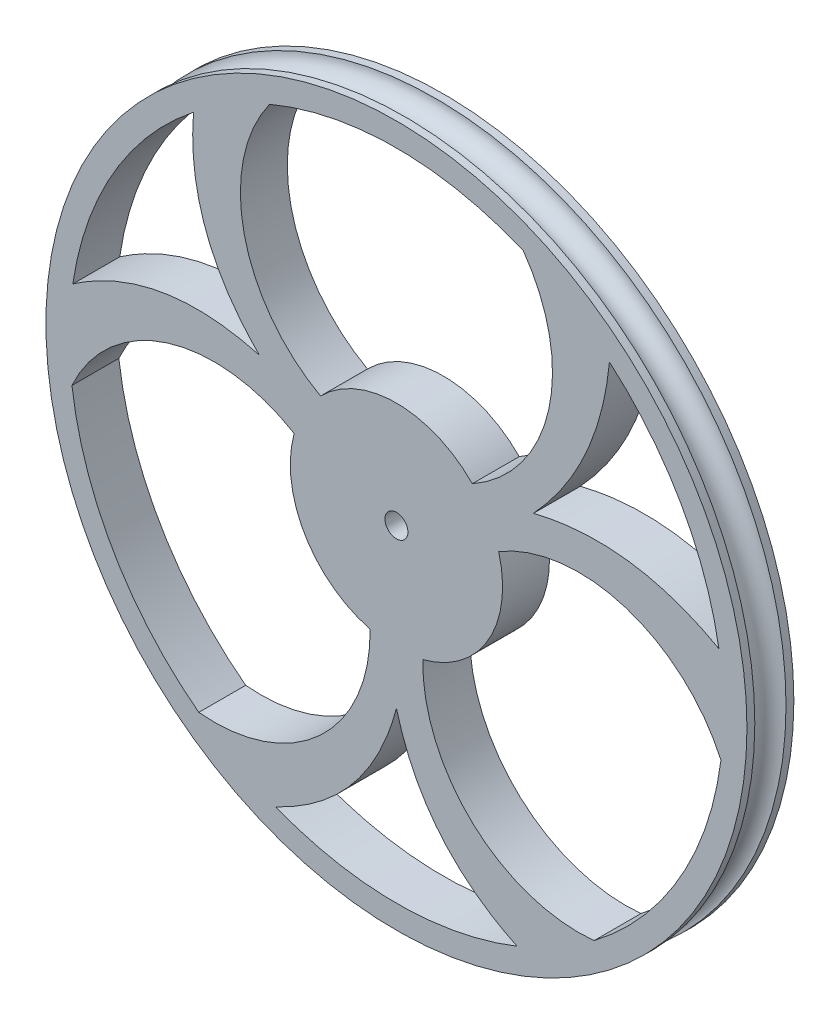
SolidWorks part; units mm, degrees
ref_plane "Front Plane" through (0, 0, 0) normal (0, 0, 1) x (1, 0, 0)
ref_plane "Top Plane" through (0, 0, 0) normal (0, 1, 0) x (1, 0, 0)
ref_plane "Right Plane" through (0, 0, 0) normal (1, 0, 0) x (0, 0, -1)
sketch "Sketch1" plane through (0, 0, 0) normal (1, 0, 0) x (0, -1, 0)
  line L0 (0, -1.7653) -> (0, 1.7653) construction
  line L2 (-43.6283, 0) -> (43.6283, 0) construction
  line L3 (-37.8968, 0) -> (37.8968, 0) construction
  circle A0 centre (39.6621, 0) radius 1.7653
  point P9 (37.8968, 0)
  point P10 (41.4274, 0)
  point P13 (39.6621, 1.7653)
  point P14 (39.6621, -1.7653)
  dimension "Width" = 3.5306
  dimension "ID" = 75.7936
sketch "Sketch4" plane through (0, 0, 0) normal (1, 0, 0) x (0, 0, -1)
  line L0 (-2.6543, -39.6621) -> (-1.7653, -39.6621)
  line L1 (1.7653, -39.6621) -> (2.6543, -39.6621)
  line L2 (-2.6543, -39.6621) -> (-2.6543, -37.0078)
  line L3 (-2.6543, -37.0078) -> (2.6543, -37.0078)
  line L4 (2.6543, -37.0078) -> (2.6543, -39.6621)
  arc A1 (1.7653, -39.6621) -> (-1.7653, -39.6621) centre (0, -39.6621) ccw
  dimension "D1" = 1.7653
  dimension "D2" = 0.889
  dimension "D3" = 5.3086
  dimension "D4" = 2.6543
  dimension "D5" = 2.6543
revolve "Revolve3" add sketch "Sketch4" angle 360 about L0
sketch "Sketch5" plane through (0, 0, 0) normal (0, 0, 1) x (1, 0, 0)
  line L0 (0, 37.8968) -> (0, -37.8968) construction
  line L2 (0, -38.94) -> (0, 38.94) construction
  arc A0 (2.9789, -11.637) -> (11.5674, 3.2387) centre (0, 0) ccw
  arc A1 (-13.2418, 35.5081) -> (-8.5885, 8.3983) centre (0, 23.8267) ccw
  arc A2 (37.3718, -6.2863) -> (11.5674, 3.2387) centre (20.6346, -11.9134) ccw
  arc A3 (-24.13, -29.2217) -> (-2.9789, -11.637) centre (-20.6346, -11.9134) ccw
  arc A4 (24.1898, 29.1723) -> (13.2418, 35.5081) centre (0, 0) ccw construction
  arc A5 (24.1898, 29.1723) -> (13.2418, 35.5081) centre (0, 0) ccw
  arc A6 (8.5885, 8.3983) -> (13.2418, 35.5081) centre (0, 23.8267) ccw
  arc A7 (2.9789, -11.637) -> (24.13, -29.2217) centre (20.6346, -11.9134) ccw
  arc A8 (-11.5674, 3.2387) -> (-37.3718, -6.2863) centre (-20.6346, -11.9134) ccw
  arc A9 (-11.5674, 3.2387) -> (-2.9789, -11.637) centre (0, 0) ccw
  arc A10 (8.5885, 8.3983) -> (-8.5885, 8.3983) centre (0, 0) ccw
  arc A11 (-13.2418, 35.5081) -> (-22.8389, 30.2415) centre (0, 0) ccw construction
  arc A12 (-13.2418, 35.5081) -> (-22.8389, 30.2415) centre (0, 0) ccw
  arc A13 (-37.6094, 4.6583) -> (-37.3718, -6.2863) centre (0, 0) ccw construction
  arc A14 (-37.6094, 4.6583) -> (-37.3718, -6.2863) centre (0, 0) ccw
  arc A15 (-24.13, -29.2217) -> (-14.7705, -34.8999) centre (0, 0) ccw construction
  arc A16 (-24.13, -29.2217) -> (-14.7705, -34.8999) centre (0, 0) ccw
  arc A17 (14.7705, -34.8999) -> (24.13, -29.2217) centre (0, 0) ccw construction
  arc A18 (14.7705, -34.8999) -> (24.13, -29.2217) centre (0, 0) ccw
  arc A19 (37.3718, -6.2863) -> (37.4801, 5.6047) centre (0, 0) ccw construction
  arc A20 (37.3718, -6.2863) -> (37.4801, 5.6047) centre (0, 0) ccw
  spline S0 degree 2 poles (0, -17.9052) (3.1827, -29.9315) (14.7705, -34.8999) knots 0 0 0 1 1 1
  spline S1 degree 2 poles (0, -17.9052) (-3.1827, -29.9315) (-14.7705, -34.8999) knots 0 0 0 1 1 1
  spline S2 degree 2 poles (-15.5064, 8.9526) (-27.5128, 12.2094) (-37.6094, 4.6583) knots 0 0 0 1 1 1
  spline S3 degree 2 poles (-15.5064, 8.9526) (-24.33, 17.7221) (-22.8389, 30.2415) knots 0 0 0 1 1 1
  spline S4 degree 2 poles (15.5064, 8.9526) (23.4309, 17.4969) (24.1898, 29.1723) knots 0 0 0 1 1 1
  spline S5 degree 2 poles (15.5064, 8.9526) (27.1411, 11.8522) (37.4801, 5.6047) knots 0 0 0 1 1 1
  point P14 (0, 0)
  point P27 (0, 0)
  dimension "D3" = 12.0122
  dimension "D2" = 9.525
  dimension "D4" = 24.13
  dimension "D1" = 3
extrude "Boss-Extrude1" add sketch "Sketch5" against normal up to surface and the other way up to surface up to face at (37.0078, 0, -2.6543) other way up to face at (39.6621, 0, 2.6543)
hole_wizard "CSK for M2 Raised Cross Head Screw1" positions "Sketch7" profile "Sketch8" countersink size "M2" standard "KS" end condition through all
sketch "Sketch7" plane through (0, 0, -2.6543) normal (0, 0, -1) x (-1, 0, 0)
  point P0 (0, 0)
sketch "Sketch8" plane through (0, 0, -2.6543) normal (1, 0, 0) x (0, 1, 0)
  line L0 (0, 0) -> (0, 5.3086)
  line L1 (0, 5.3086) -> (1.3, 5.3086)
  line L2 (1.3, 5.3086) -> (1.3, 0.9657)
  line L3 (1.3, 0.9657) -> (2.3, 0)
  line L5 (2.3, 0) -> (0, 0)
  line L6 (-1.3, 0.9657) -> (-2.3, 0) construction
  line L11 (0, -6.35) -> (0, 107.95) construction
  dimension "Thru Hole Dia." = 2.6
  dimension "Thru Hole Depth" = 5.3086
  dimension "Near C'Sink Dia." = 4.6
  dimension "Near C'Sink Angle" = 92
